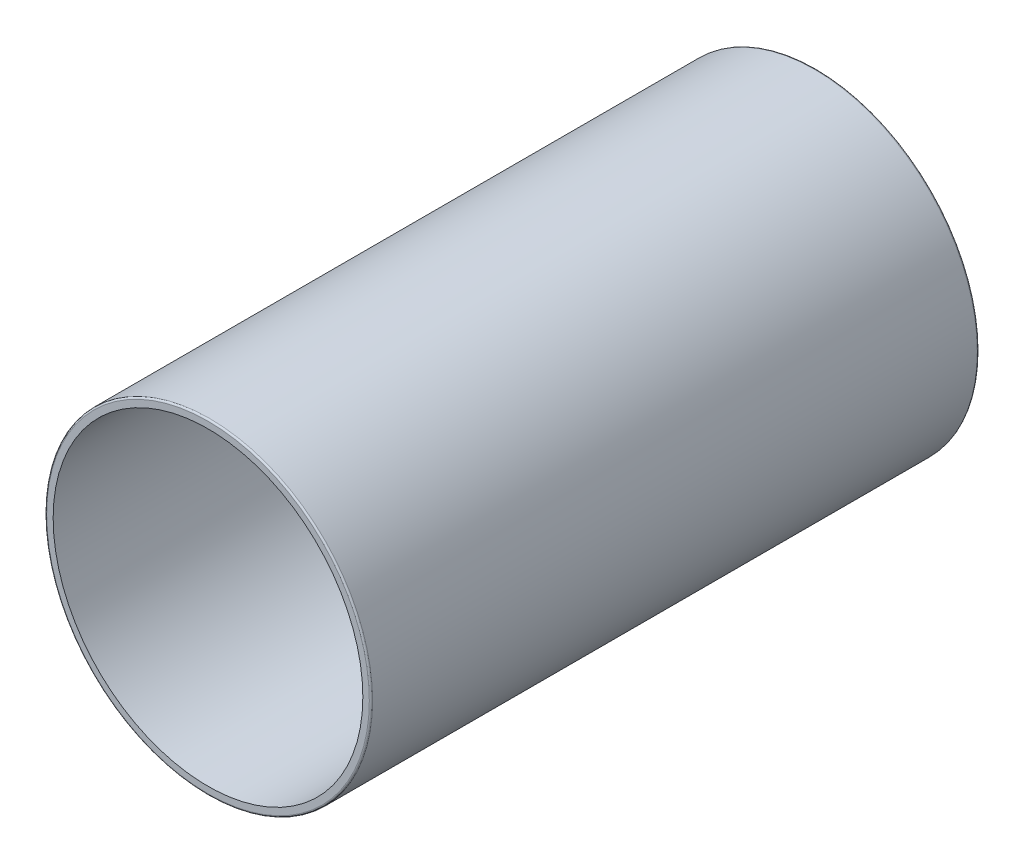
SolidWorks part; units mm, degrees
ref_plane "Front Plane" through (0, 0, 0) normal (0, 0, 1) x (1, 0, 0)
ref_plane "Top Plane" through (0, 0, 0) normal (0, 1, 0) x (1, 0, 0)
ref_plane "Right Plane" through (0, 0, 0) normal (1, 0, 0) x (0, 0, -1)
sketch "Sketch2" plane through (0, 0, 0) normal (0, 0, 1) x (1, 0, 0)
  circle A0 centre (0, 0) radius 201
extrude "Boss-Extrude1" add sketch "Sketch2" along normal blind 750
shell "Shell1" thickness 10
sketch "Sketch3" plane through (0, 0, 10) normal (0, 0, 1) x (1, 0, 0)
  circle A0 centre (0, 0) radius 192.25
extrude "Cut-Extrude1" cut sketch "Sketch3" against normal through all
fillet "Fillet2" radius 2 1 edges at (201, 0, 0)
fillet "Fillet3" radius 2 1 edges at (201, 0, 750)
